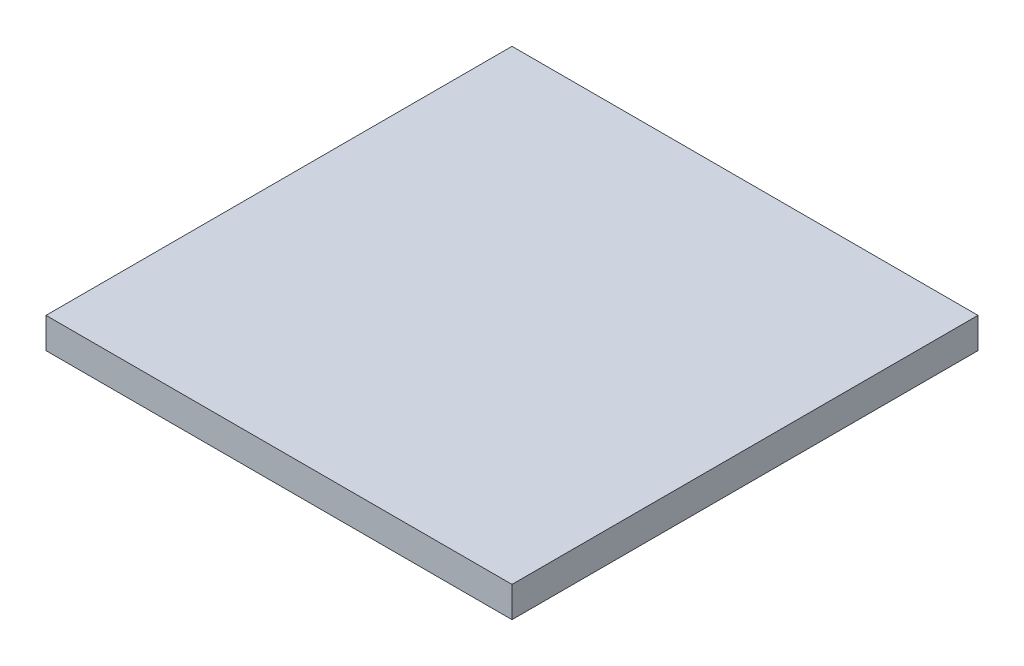
SolidWorks part; units mm, degrees
material "2024-T3"
ref_plane "Front Plane" through (0, 0, 0) normal (0, 0, 1) x (1, 0, 0)
ref_plane "Top Plane" through (0, 0, 0) normal (0, 1, 0) x (1, 0, 0)
ref_plane "Right Plane" through (0, 0, 0) normal (1, 0, 0) x (0, 0, -1)
sketch "Sketch1" plane through (0, 0, 0) normal (0, 1, 0) x (1, 0, 0)
  line L1 (-76.2, -76.2) -> (76.2, -76.2)
  line L2 (-76.2, -76.2) -> (-76.2, 76.2)
  line L3 (-76.2, 76.2) -> (76.2, 76.2)
  line L4 (76.2, -76.2) -> (76.2, 76.2)
  line L5 (0, 76.2) -> (0, -76.2) construction
  line L6 (-76.2, 0) -> (76.2, 0) construction
  point P0 (0, 0)
  dimension "D1" = 152.4
  dimension "D2" = 152.4
extrude "Boss-Extrude1" add sketch "Sketch1" along normal blind 10
